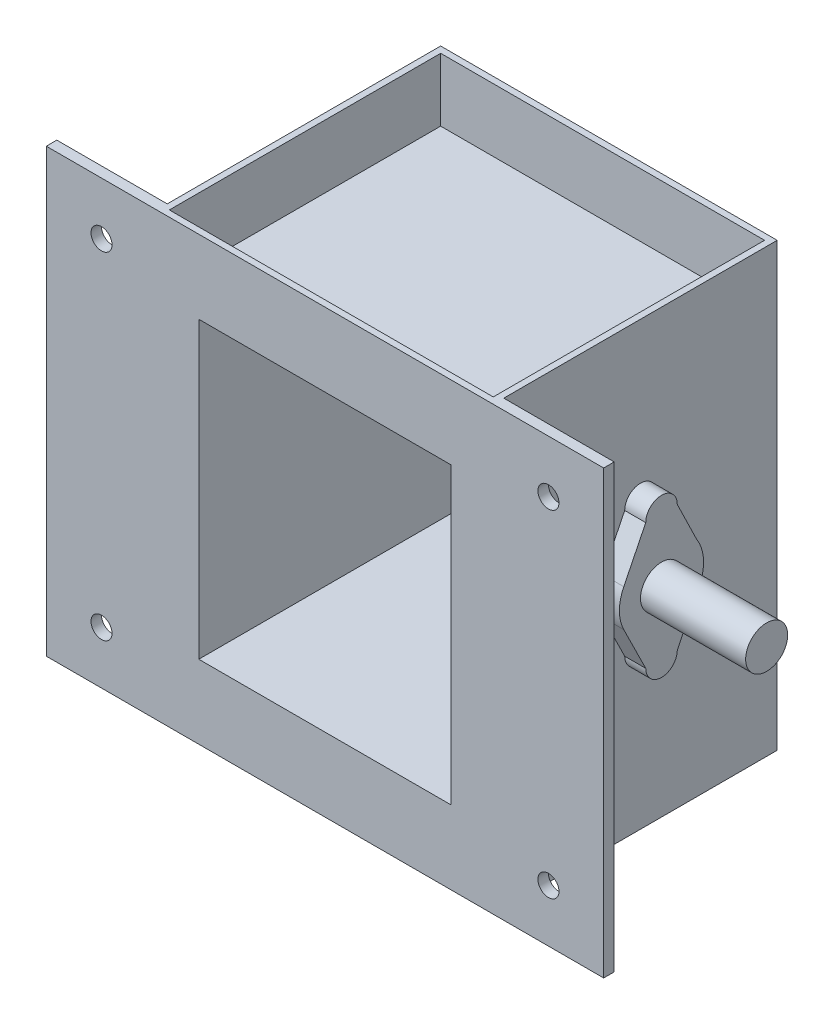
SolidWorks part; units mm, degrees
ref_plane "Plan de face" through (0, 0, 0) normal (0, 0, 1) x (1, 0, 0)
ref_plane "Plan de dessus" through (0, 0, 0) normal (0, 1, 0) x (1, 0, 0)
ref_plane "Plan de droite" through (0, 0, 0) normal (1, 0, 0) x (0, 0, -1)
sketch "Esquisse1" plane through (0, 0, 0) normal (0, 0, 1) x (1, 0, 0)
  line L1 (-80, -105) -> (80, -105)
  line L2 (-80, -105) -> (-80, 105)
  line L3 (-80, 105) -> (80, 105)
  line L4 (80, -105) -> (80, 105)
  line L5 (-80, -105) -> (80, 105) construction
  line L6 (-80, 105) -> (80, -105) construction
  point P0 (0, 0)
  dimension "D1" = 210
  dimension "D2" = 160
extrude "Boss.-Extru.1" add sketch "Esquisse1" along normal blind 135
sketch "Esquisse2" plane through (0, 0, 135) normal (0, 0, 1) x (1, 0, 0)
  line L1 (-132.5, -105) -> (132.5, -105)
  line L2 (-132.5, -105) -> (-132.5, 105)
  line L3 (-132.5, 105) -> (132.5, 105)
  line L4 (132.5, -105) -> (132.5, 105)
  line L5 (-132.5, -105) -> (132.5, 105) construction
  line L6 (-132.5, 105) -> (132.5, -105) construction
  point P0 (0, 0)
  dimension "D1" = 265
  dimension "D2" = 210
extrude "Boss.-Extru.2" add sketch "Esquisse2" against normal blind 5
sketch "Esquisse4" plane through (80, 0, 0) normal (1, 0, 0) x (0, 0, -1)
  line L0 (0, 105) -> (-130, -105) construction
  circle A0 centre (-65, 0) radius 10
  dimension "D1" = 20
extrude "Boss.-Extru.3" add sketch "Esquisse4" along normal blind 60
mirror "Symétrie1" about plane through (0, 0, 0) normal (1, 0, 0) of "Boss.-Extru.3"
sketch "Esquisse5" plane through (80, 0, 0) normal (1, 0, 0) x (0, 0, -1)
  line L0 (-57.5, 30) -> (-48.2184, 10.8801)
  line L1 (-57.5, -30) -> (-47.0643, -8.8494)
  line L2 (-72.5, 30) -> (-82.9357, 8.8494)
  line L3 (-72.5, -30) -> (-82.9357, -8.8494)
  arc A0 (-82.9357, 8.8494) -> (-82.9357, -8.8494) centre (-65, 0) ccw
  arc A1 (-57.5, 30) -> (-72.5, 30) centre (-65, 30) ccw
  arc A2 (-72.5, -30) -> (-57.5, -30) centre (-65, -30) ccw
  arc A3 (-47.0643, -8.8494) -> (-48.2184, 10.8801) centre (-65, 0) ccw
  dimension "D3" = 15
  dimension "D4" = 15
  dimension "D5" = 40
  dimension "D1" = 30
  dimension "D2" = 30
extrude "Boss.-Extru.4" add sketch "Esquisse5" along normal blind 10
mirror "Symétrie2" about plane through (0, 0, 0) normal (1, 0, 0) of "Boss.-Extru.4"
sketch "Esquisse6" plane through (0, 105, 0) normal (0, 1, 0) x (1, 0, 0)
  line L0 (-80, 0) -> (80, -135) construction
  line L1 (132.5, -135) -> (-132.5, -135) construction
  line L2 (80, 0) -> (-80, 0) construction
  line L3 (-77, -132) -> (77, -132)
  line L4 (-77, -132) -> (-77, -3)
  line L5 (-77, -3) -> (77, -3)
  line L6 (77, -132) -> (77, -3)
  line L7 (-77, -132) -> (77, -3) construction
  line L8 (-77, -3) -> (77, -132) construction
  line L9 (80, -130) -> (80, 0) construction
  line L10 (0, 0) -> (0, -154.1058) construction
  point P5 (0, -67.5)
  dimension "D1" = 3
  dimension "D2" = 3
extrude "Enlèv. mat.-Extru.2" cut sketch "Esquisse6" against normal blind 30
mirror "Symétrie3" about plane through (0, 0, 0) normal (0, 1, 0) of "Enlèv. mat.-Extru.2"
sketch "Esquisse7" plane through (0, 0, 0) normal (0, 0, -1) x (-1, 0, 0)
  line L1 (60, 70) -> (-60, 70)
  line L2 (60, 70) -> (60, -70)
  line L3 (60, -70) -> (-60, -70)
  line L4 (-60, 70) -> (-60, -70)
  line L5 (60, 70) -> (-60, -70) construction
  line L6 (60, -70) -> (-60, 70) construction
  point P0 (0, 0)
  dimension "D1" = 120
  dimension "D2" = 140
extrude "Enlèv. mat.-Extru.3" cut sketch "Esquisse7" against normal blind 150
sketch "Esquisse9" plane through (0, 0, 130) normal (0, 0, -1) x (-1, 0, 0)
  line L0 (-106.25, 105) -> (-106.25, -105) construction
  line L1 (-132.5, 105) -> (-80, 105) construction
  line L2 (-80, -105) -> (-132.5, -105) construction
  circle A0 centre (-106.25, 80) radius 5
  circle A1 centre (-106.25, -80) radius 5
  dimension "D1" = 10
  dimension "D2" = 10
  dimension "D3" = 160
  dimension "D4" = 25
extrude "Enlèv. mat.-Extru.4" cut sketch "Esquisse9" against normal blind 150
mirror "Symétrie4" about plane through (0, 0, 0) normal (1, 0, 0) of "Enlèv. mat.-Extru.4"
